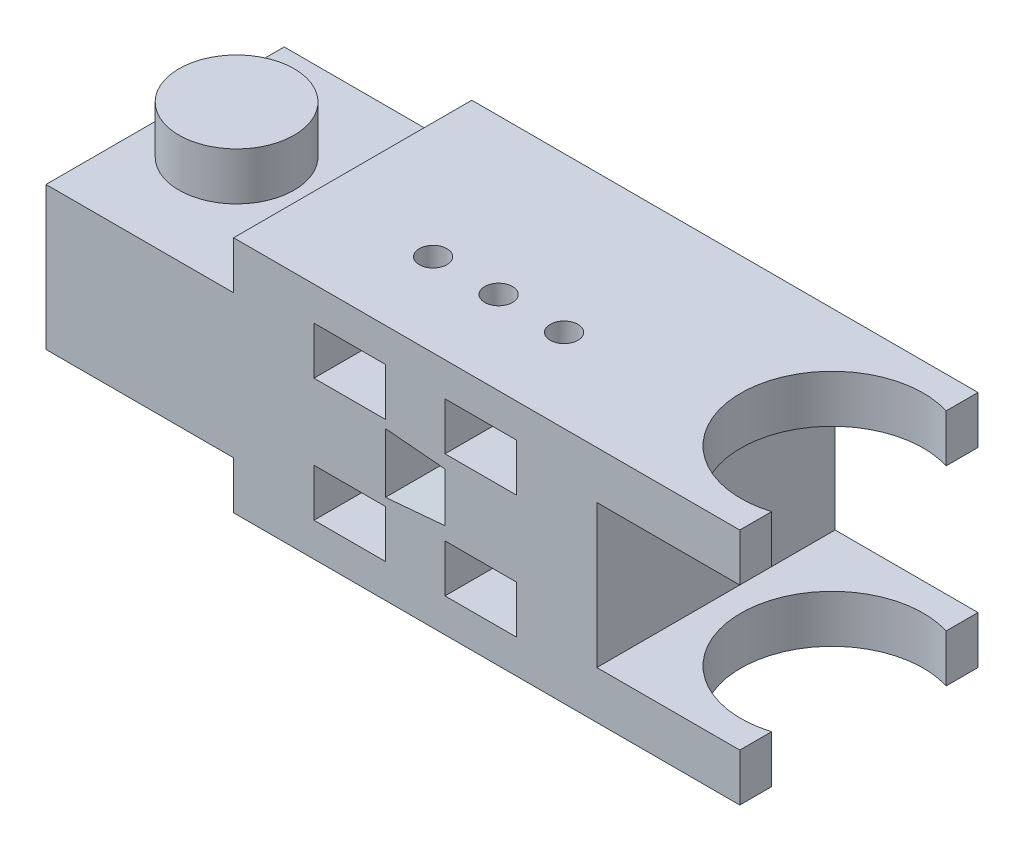
SolidWorks part; units mm, degrees
ref_plane "Front Plane" through (0, 0, 0) normal (0, 0, 1) x (1, 0, 0)
ref_plane "Top Plane" through (0, 0, 0) normal (0, 1, 0) x (1, 0, 0)
ref_plane "Right Plane" through (0, 0, 0) normal (1, 0, 0) x (0, 0, -1)
sketch "Sketch1" plane through (0, 0, 0) normal (0, 0, 1) x (1, 0, 0)
  line L0 (0, 0) -> (-19.5, 0) construction
  line L5 (-19.5, 0) -> (-30.5, 0) construction
  line L6 (-30.5, 0) -> (-50, 0) construction
  line L7 (-50, -6) -> (-42.5, -6) construction
  line L8 (-50, -10) -> (0, -10) construction
  line L9 (-50, -10) -> (-50, 10) construction
  line L10 (-50, 10) -> (0, 10) construction
  line L11 (0, -10) -> (0, 10) construction
  line L12 (-50, -10) -> (0, 10) construction
  line L13 (-50, 10) -> (0, -10) construction
  line L14 (-40.25, -10) -> (-40.25, -6)
  line L15 (-40.25, -6) -> (-50, -6)
  line L16 (-40.25, 10) -> (-40.25, 6)
  line L17 (-40.25, 6) -> (-50, 6)
  line L18 (-50, 6) -> (-56, 6)
  line L19 (-56, 6) -> (-56, -6)
  line L20 (-56, -6) -> (-50, -6)
  line L21 (-40.25, 10) -> (0, 10) construction
  line L22 (-40.25, -10) -> (0, -10)
  line L23 (0, 10) -> (2.25, 10)
  line L24 (2.25, 10) -> (2.25, 6)
  line L25 (2.25, 6) -> (0, 6)
  line L26 (0, -10) -> (2.25, -10)
  line L27 (2.25, -10) -> (2.25, -6)
  line L28 (2.25, -6) -> (0, -6)
  line L29 (0, 6) -> (0, -6) construction
  line L30 (0, 6) -> (-9.75, 6)
  line L31 (-9.75, 6) -> (-9.75, -6)
  line L32 (-9.75, -6) -> (0, -6)
  line L33 (-7.5, 0) -> (0, 0) construction
  line L34 (-7.5, 0) -> (-9.75, 0) construction
  line L35 (-40.25, 10) -> (0, 10)
  line L36 (0, 0) -> (2.25, 0) construction
  line L37 (2.25, 0) -> (2.25, 6) construction
  line L38 (-42.5, -6) -> (-40.25, -6) construction
  point P2 (-25, 0)
  dimension "D2" = 19.5
  dimension "D3" = 11
  dimension "D4" = 19.5
  dimension "D6" = 20
  dimension "D7" = 4
  dimension "D8" = 4
  dimension "D1" = 7.5
  dimension "D9" = 2.25
  dimension "D10" = 6
  dimension "D5" = 7.5
  dimension "D11" = 2.25
  dimension "D12" = 2.25
extrude "Boss-Extrude1" add sketch "Sketch1" along normal blind 20
sketch "Sketch2" plane through (0, -6, 0) normal (0, -1, 0) x (1, 0, 0)
  line L0 (-50, 0) -> (0, 0) construction
  line L1 (-50, 0) -> (0, 0) construction
  line L2 (-50, 0) -> (-50, 20) construction
  line L3 (-56, 20) -> (-40.25, 20) construction
  circle A0 centre (-50, 10) radius 4.835
  dimension "D1" = 9.67
extrude "Boss-Extrude2" add sketch "Sketch2" along normal blind 4
sketch "Sketch3" plane through (0, -10, 0) normal (0, -1, 0) x (1, 0, 0)
  line L0 (0, 0) -> (0, 20) construction
  line L1 (-40.25, 20) -> (2.25, 20) construction
  circle A0 centre (0, 10) radius 7.665
  dimension "D1" = 15.33
extrude "Cut-Extrude1" cut sketch "Sketch3" against normal up to surface (20 mm away) up to face at (-19, 10, 10)
mirror "Mirror1" about plane through (0, 0, 0) normal (0, 1, 0) of "Boss-Extrude2"
sketch "Sketch4" plane through (0, 0, 20) normal (0, 0, 1) x (1, 0, 0)
  line L0 (0, -10) -> (0, 10) construction
  line L1 (0, -10) -> (0, 10) construction
  line L2 (0, 0) -> (-25, 0) construction
  line L3 (-19.5, 0) -> (-30.5, 0) construction
  line L4 (-27.5, 2.5) -> (-22.5, 2.0626)
  line L5 (-27.5, -2.5) -> (-22.5, -2.5) construction
  line L6 (-27.5, -2.5) -> (-27.5, 2.5)
  line L7 (-27.5, 2.5) -> (-22.5, 2.5) construction
  line L8 (-22.5, -2.5) -> (-22.5, 2.5) construction
  line L9 (-27.5, -2.5) -> (-22.5, 2.5) construction
  line L10 (-27.5, 2.5) -> (-22.5, -2.5) construction
  line L11 (-27.5, -2.5) -> (-22.5, -2.0626)
  line L12 (-22.5, 2.0626) -> (-22.5, -2.0626)
  dimension "D1" = 5
  dimension "D2" = 5
  dimension "D3" = 25
  dimension "D4" = 5
  dimension "D5" = 5
extrude "Cut-Extrude2" cut sketch "Sketch4" against normal blind 10
sketch "Sketch5" plane through (0, 0, 20) normal (0, 0, 1) x (1, 0, 0)
  line L0 (-30.5, 0) -> (-50, 0) construction
  line L1 (-19.5, 0) -> (-30.5, 0) construction
  line L2 (0, 0) -> (-19.5, 0) construction
  line L3 (-30.5, 0) -> (-50, 0) construction
  line L4 (-19.5, 0) -> (-30.5, 0) construction
  line L5 (0, 0) -> (-19.5, 0) construction
  line L6 (-30.5, -5.165) -> (-30.5, 5.165) construction
  line L7 (-19.5, -5.165) -> (-19.5, 5.165) construction
  line L9 (-33.5, 7.165) -> (-27.5, 7.165)
  line L10 (-33.5, 7.165) -> (-33.5, 3.165)
  line L11 (-33.5, 3.165) -> (-27.5, 3.165)
  line L12 (-27.5, 7.165) -> (-27.5, 3.165)
  line L13 (-33.5, 7.165) -> (-27.5, 3.165) construction
  line L14 (-33.5, 3.165) -> (-27.5, 7.165) construction
  line L15 (-22.5, 7.165) -> (-16.5, 7.165)
  line L16 (-22.5, 7.165) -> (-22.5, 3.165)
  line L17 (-22.5, 3.165) -> (-16.5, 3.165)
  line L18 (-16.5, 7.165) -> (-16.5, 3.165)
  line L19 (-22.5, 7.165) -> (-16.5, 3.165) construction
  line L20 (-22.5, 3.165) -> (-16.5, 7.165) construction
  line L21 (-22.5, -7.165) -> (-16.5, -7.165)
  line L22 (-22.5, -7.165) -> (-22.5, -3.165)
  line L23 (-22.5, -3.165) -> (-16.5, -3.165)
  line L24 (-16.5, -7.165) -> (-16.5, -3.165)
  line L25 (-22.5, -7.165) -> (-16.5, -3.165) construction
  line L26 (-22.5, -3.165) -> (-16.5, -7.165) construction
  line L27 (-33.5, -7.165) -> (-27.5, -7.165)
  line L28 (-33.5, -7.165) -> (-33.5, -3.165)
  line L29 (-33.5, -3.165) -> (-27.5, -3.165)
  line L30 (-27.5, -7.165) -> (-27.5, -3.165)
  line L31 (-33.5, -7.165) -> (-27.5, -3.165) construction
  line L32 (-33.5, -3.165) -> (-27.5, -7.165) construction
  point P7 (-30.5, 0)
  point P10 (-19.5, 0)
  dimension "D1" = 4
  dimension "D2" = 6
  dimension "D3" = 6.33
extrude "Cut-Extrude3" cut sketch "Sketch5" against normal blind 10
sketch "Sketch6" plane through (0, -10, 0) normal (0, -1, 0) x (1, 0, 0)
  line L0 (-22.5, 10) -> (-16.5, 10) construction
  line L1 (-27.5, 10) -> (-22.5, 10) construction
  line L2 (-33.5, 10) -> (-27.5, 10) construction
  line L3 (-22.5, 10) -> (-16.5, 10) construction
  line L4 (-27.5, 10) -> (-22.5, 10) construction
  line L5 (-33.5, 10) -> (-27.5, 10) construction
  line L6 (-30.5, 10) -> (-30.5, 13) construction
  line L7 (-25, 10) -> (-25, 13) construction
  line L8 (-19.5, 10) -> (-19.5, 13) construction
  circle A0 centre (-30.5, 13) radius 1.165
  circle A1 centre (-25, 13) radius 1.165
  circle A2 centre (-19.5, 13) radius 1.165
  dimension "D2" = 2.33
  dimension "D1" = 3
extrude "Cut-Extrude4" cut sketch "Sketch6" against normal up to surface (20 mm away) up to face at (-13.5692, 10, 10)
equation "\"offset\"=5"
equation "\"x_0\"= 19.5"
equation "\"D2@Sketch1\"=\"x_0\""
equation "\"x_1\"= 11"
equation "\"D3@Sketch1\"=\"x_1\""
equation "\"x_2\"= 19.5"
equation "\"D4@Sketch1\"=\"x_2\""
equation "\"bearing_width\"= 4"
equation "\"link_width\"= 20"
equation "\"link_height\"= 20"
equation "\"D6@Sketch1\"=\"link_width\""
equation "\"D7@Sketch1\"=\"bearing_width\""
equation "\"D8@Sketch1\"=\"bearing_width\""
equation "\"D1@Boss-Extrude1\"=\"link_height\""
equation "\"D1@Boss-Extrude2\"=\"bearing_width\""
equation "\"bearing_OD\"=15"
equation "\"bearing_ID\"=10"
equation "\"D1@Sketch3\"=\"bearing_OD\"+\"tol\""
equation "\"D1@Sketch1\"=\"bearing_OD\"/2"
equation "\"bearing_offset\"= 2.25"
equation "\"D9@Sketch1\"=\"bearing_offset\""
equation "\"bearing_backstop_offset\"=6"
equation "\"D10@Sketch1\"=\"bearing_backstop_offset\""
equation "\"D5@Sketch1\"=\"bearing_OD\"/2"
equation "\"D11@Sketch1\"=\"bearing_offset\""
equation "\"D12@Sketch1\"=\"bearing_offset\""
equation "\"chuck_width\"=5"
equation "\"D4@Sketch4\"=\"chuck_width\""
equation "\"chuck_angle\"=5"
equation "\"D2@Sketch4\"=\"chuck_angle\""
equation "\"D1@Sketch4\"=\"chuck_angle\""
equation "\"chuck_length\"=5"
equation "\"chuck_depth\"= 10"
equation "\"D1@Cut-Extrude2\"=\"chuck_depth\""
equation "\"D5@Sketch4\"=\"chuck_length\""
equation "\"chuck_distance\"=25"
equation "\"D3@Sketch4\"=\"chuck_distance\""
equation "\"post_width\"=4"
equation "\"D1@Sketch5\"=\"post_width\""
equation "\"post_length\"=6"
equation "\"D2@Sketch5\"=\"post_length\""
equation "\"post_bearing_width\"=6"
equation "\"D3@Sketch5\"=\"post_bearing_width\"+\"tol\""
equation "\"post_depth\"=10"
equation "\"D1@Cut-Extrude3\"=\"post_depth\""
equation "\"pin_offset\"= 3"
equation "\"D1@Sketch6\"=\"pin_offset\""
equation "\"pin_dia\"=2"
equation "\"D2@Sketch6\"=\"pin_dia\"+\"tol\""
equation "\"D1@Sketch2\"=\"bearing_ID\"-\"tol\""
equation "\"tol\"= 0.33"
equation "\"D1@Sketch8\"=4.00mm+\"tol\""
equation "\"D1@Sketch12\"=\"tol\"/2"
